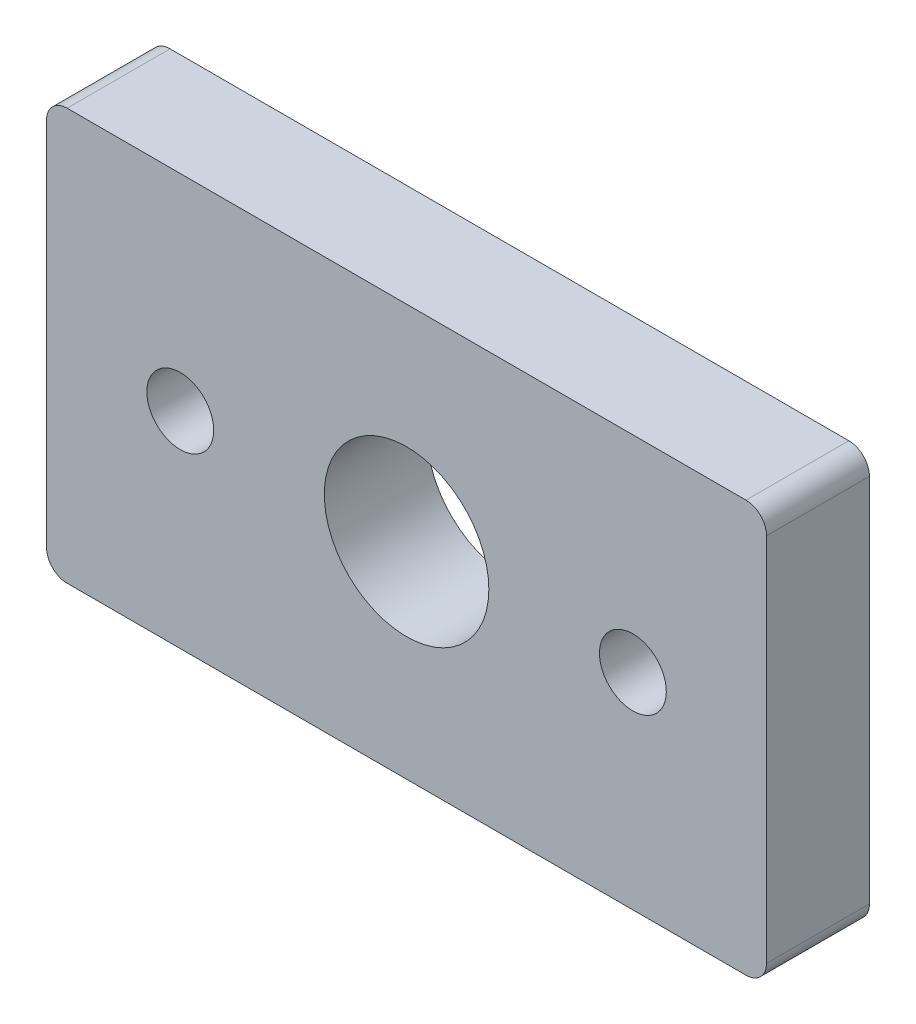
SolidWorks part; units mm, degrees
material "Acrylic (Medium-high impact)"
ref_plane "Front Plane" through (0, 0, 0) normal (0, 0, 1) x (1, 0, 0)
ref_plane "Top Plane" through (0, 0, 0) normal (0, 1, 0) x (1, 0, 0)
ref_plane "Right Plane" through (0, 0, 0) normal (1, 0, 0) x (0, 0, -1)
sketch "Sketch1" plane through (0, 0, 0) normal (0, 0, 1) x (1, 0, 0)
  line L0 (0, 10) -> (35, 10) construction
  line L1 (0, 0) -> (35, 0)
  line L2 (0, 0) -> (0, 20)
  line L3 (0, 20) -> (35, 20)
  line L4 (35, 0) -> (35, 20)
  line L5 (17.5, 20) -> (17.5, 0) construction
  circle A0 centre (17.5, 10) radius 4
  circle A1 centre (28.5, 10) radius 1.625
  circle A2 centre (6.5, 10) radius 1.625
  point P11 (17.5, 10)
  dimension "D3" = 8
  dimension "D4" = 3.25
  dimension "D1" = 35
  dimension "D2" = 20
  dimension "D5" = 11
extrude "Boss-Extrude1" add sketch "Sketch1" along normal blind 5
fillet "Fillet1" radius 1 4 edges at (35, 0, 2.5) (0, 0, 2.5) (35, 20, 2.5) (0, 20, 2.5)
